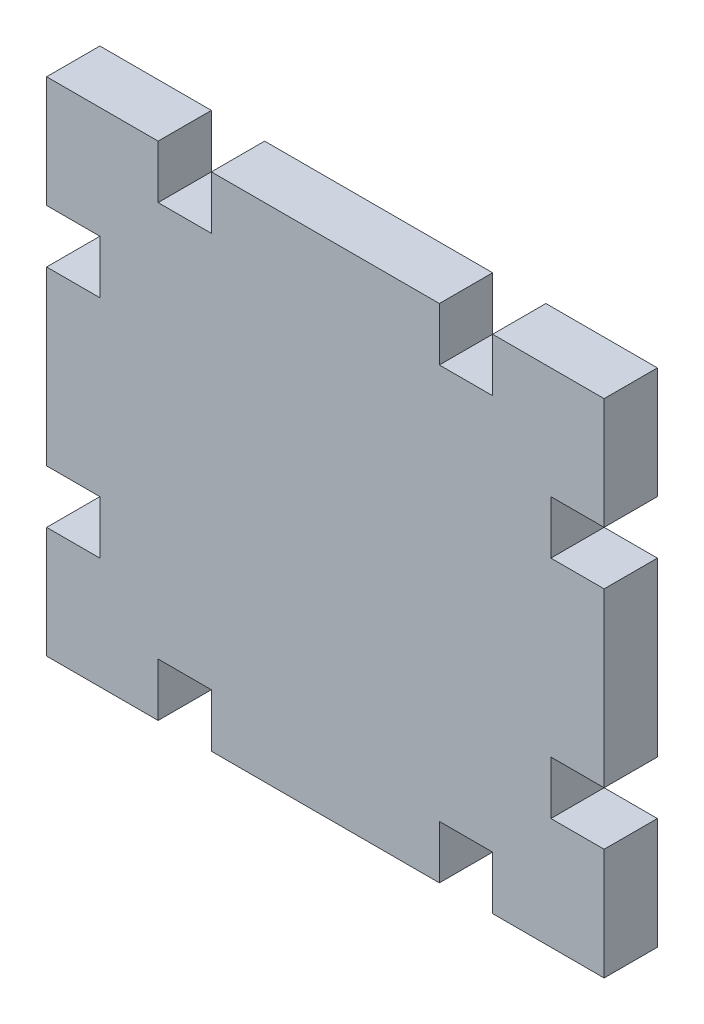
SolidWorks part; units mm, degrees
ref_plane "Front Plane" through (0, 0, 0) normal (0, 0, 1) x (1, 0, 0)
ref_plane "Top Plane" through (0, 0, 0) normal (0, 1, 0) x (1, 0, 0)
ref_plane "Right Plane" through (0, 0, 0) normal (1, 0, 0) x (0, 0, -1)
sketch "Sketch3" plane through (0, 0, 0) normal (0, 0, 1) x (1, 0, 0)
  line L29 (0, 0) -> (0, 22.5) construction
  line L30 (0, 0) -> (50, 0) construction
  line L31 (0, 0) -> (25, 0) construction
  line L32 (0, 0) -> (10, 0) construction
  line L33 (10, 0) -> (10, 4.7752)
  line L34 (10, 4.7752) -> (14.7752, 4.7752)
  line L35 (14.7752, 4.7752) -> (14.7752, 0)
  line L36 (25, 0) -> (25, 4.7752) construction
  line L37 (25, 4.7752) -> (15, 4.7752) construction
  line L42 (10, 0) -> (0, 0)
  line L43 (14.7752, 0) -> (25, 0)
  line L47 (35.2248, 4.7752) -> (35.2248, 0)
  line L48 (40, 0) -> (40, 4.7752)
  line L49 (40, 4.7752) -> (35.2248, 4.7752)
  line L50 (25, 0) -> (35.2248, 0)
  line L52 (40, 0) -> (50, 0)
  line L53 (0, 22.5) -> (50, 22.5) construction
  line L67 (0, 45) -> (0, 0) construction
  line L72 (50, 45) -> (50, 0) construction
  line L73 (50, 45) -> (50, 35)
  line L74 (50, 35) -> (45.2248, 35)
  line L75 (45.2248, 35) -> (45.2248, 30.2248)
  line L76 (45.2248, 30.2248) -> (50, 30.2248)
  line L77 (50, 30.2248) -> (50, 22.5)
  line L78 (45.2248, 14.7752) -> (50, 14.7752)
  line L79 (45.2248, 10) -> (45.2248, 14.7752)
  line L80 (50, 10) -> (45.2248, 10)
  line L81 (50, 22.5) -> (50, 14.7752)
  line L82 (50, 10) -> (50, 0)
  line L83 (0, 22.5) -> (25, 22.5) construction
  line L84 (25, 22.5) -> (25, 0) construction
  line L85 (0, 10) -> (4.7752, 10)
  line L86 (4.7752, 10) -> (4.7752, 14.7752)
  line L87 (4.7752, 14.7752) -> (0, 14.7752)
  line L88 (4.7752, 30.2248) -> (0, 30.2248)
  line L89 (0, 35) -> (4.7752, 35)
  line L90 (4.7752, 35) -> (4.7752, 30.2248)
  line L91 (0, 35) -> (0, 45)
  line L92 (0, 10) -> (0, 0)
  line L93 (0, 30.2248) -> (0, 14.7752)
  line L94 (40, 45) -> (40, 40.2248)
  line L95 (35.2248, 40.2248) -> (35.2248, 45)
  line L96 (40, 40.2248) -> (35.2248, 40.2248)
  line L97 (10, 40.2248) -> (14.7752, 40.2248)
  line L98 (14.7752, 40.2248) -> (14.7752, 45)
  line L99 (10, 45) -> (10, 40.2248)
  line L100 (10, 45) -> (0, 45)
  line L101 (14.7752, 45) -> (35.2248, 45)
  line L102 (40, 45) -> (50, 45)
  point P1 (0, 0)
  dimension "D1" = 50
  dimension "D2" = 25
  dimension "D3" = 10
  dimension "D4" = 4.7752
  dimension "D5" = 4.7752
  dimension "D7" = 10
  dimension "D8" = 22.5
  dimension "D9" = 10
  dimension "D10" = 10
  dimension "D6" = 4.7752
  dimension "D11" = 10
  dimension "D12" = 4.7752
  dimension "D13" = 4.7752
  dimension "D14" = 10
extrude "Boss-Extrude1" add sketch "Sketch3" against normal blind 4.7752
